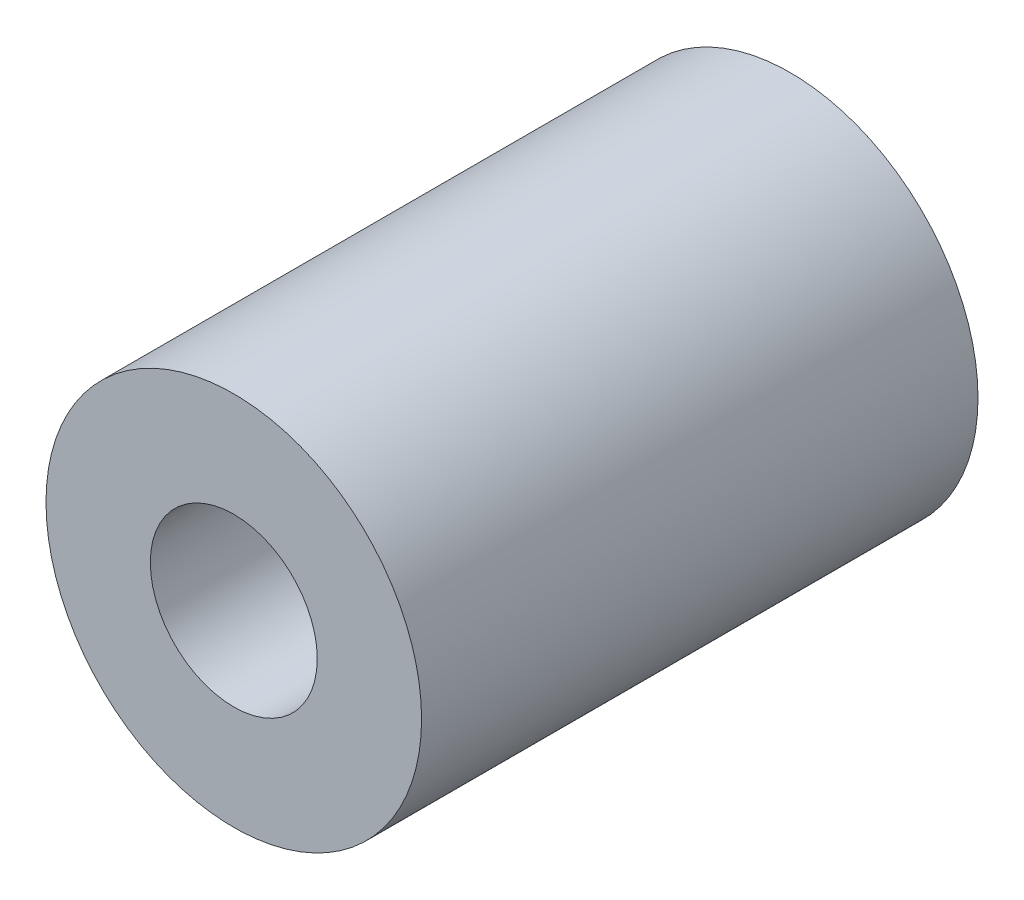
SolidWorks part; units mm, degrees
ref_plane "Front Plane" through (0, 0, 0) normal (0, 0, 1) x (1, 0, 0)
ref_plane "Top Plane" through (0, 0, 0) normal (0, 1, 0) x (1, 0, 0)
ref_plane "Right Plane" through (0, 0, 0) normal (1, 0, 0) x (0, 0, -1)
sketch "Sketch2" plane through (0, 0, 0) normal (0, 0, 1) x (1, 0, 0)
  circle A0 centre (0, 0) radius 13.5
  dimension "D1" = 27
extrude "Boss-Extrude1" add sketch "Sketch2" along normal blind 40
sketch "Sketch3" plane through (0, 0, 40) normal (0, 0, 1) x (1, 0, 0)
  circle A0 centre (0, 0) radius 6
  dimension "D1" = 12
extrude "Cut-Extrude1" cut sketch "Sketch3" against normal blind 40
